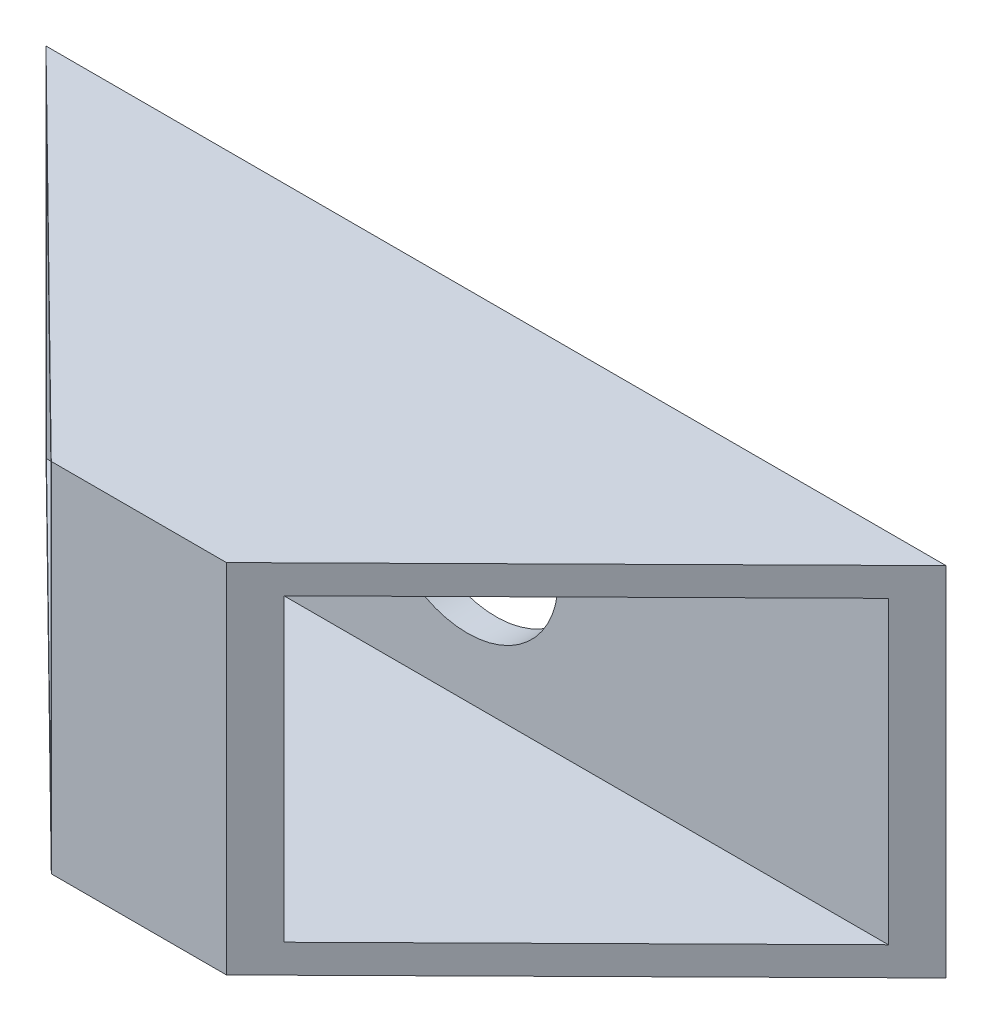
SolidWorks part; units mm, degrees
ref_plane "Front Plane" through (0, 0, 0) normal (0, 0, 1) x (1, 0, 0)
ref_plane "Top Plane" through (0, 0, 0) normal (0, 1, 0) x (1, 0, 0)
ref_plane "Right Plane" through (0, 0, 0) normal (1, 0, 0) x (0, 0, -1)
sketch "Sketch1" plane through (0, 0, 0) normal (0, 1, 0) x (1, 0, 0)
  line L0 (-17.3503, 15.9578) -> (45.6497, 15.9578)
  line L1 (8.0197, -9.0422) -> (20.2797, -9.0422)
  line L3 (-17.3503, 15.9578) -> (8.0197, -9.0422)
  line L4 (45.6497, 15.9578) -> (20.2797, -9.0422)
  dimension "D1" = 63
  dimension "D2" = 12.26
  dimension "D3" = 25
  dimension "D4" = 44.579
  dimension "D5" = 44.579
extrude "Boss-Extrude1" add sketch "Sketch1" along normal blind 25
shell "Shell1" thickness 2
sketch "Sketch2" plane through (0, 0, -15.9578) normal (0, 0, -1) x (-1, 0, 0)
  line L0 (17.3503, 0) -> (-45.6497, 25) construction
  circle A0 centre (-14.1497, 12.5) radius 6.35
  dimension "D1" = 12.7
extrude "Cut-Extrude1" cut sketch "Sketch2" against normal blind 10 contours A0
